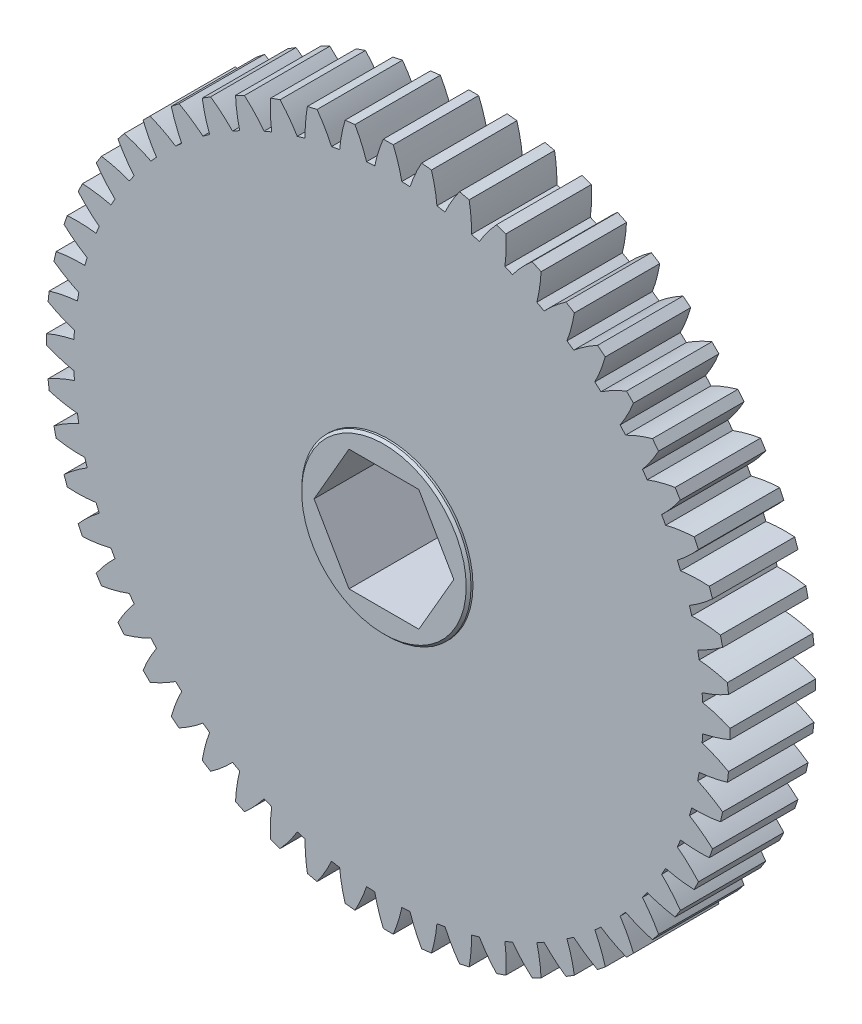
SolidWorks part; units mm, degrees
material "AISI 4130 Steel, normalized at 870C"
ref_plane "Front Plane" through (0, 0, 0) normal (0, 0, 1) x (1, 0, 0)
ref_plane "Top Plane" through (0, 0, 0) normal (0, 1, 0) x (1, 0, 0)
ref_plane "Right Plane" through (0, 0, 0) normal (1, 0, 0) x (0, 0, -1)
sketch "Sketch1" plane through (0, 0, 0) normal (0, 0, 1) x (1, 0, 0)
  circle A0 centre (0, 0) radius 33.02
  dimension "D1" = 66.04
extrude "Extrude1" add sketch "Sketch1" along normal mid plane 8.9662
sketch "Sketch2" plane through (0, 0, -4.4831) normal (0, 0, -1) x (-1, 0, 0)
  line L0 (35.8775, 0.5187) -> (35.8775, -0.5187)
  line L1 (35.8775, 0) -> (33.02, 0) construction
  arc A0 (35.8775, 0.5187) -> (32.9894, 1.4209) centre (29.9148, -13.4957) ccw
  arc A1 (32.9894, -1.4209) -> (35.8775, -0.5187) centre (29.9148, 13.4957) ccw
  circle A2 centre (0, 0) radius 33.02 construction
  arc A3 (32.9894, -1.4209) -> (32.9894, 1.4209) centre (0, 0) ccw
  dimension "D4" = 15.2301
  dimension "D1" = 1.0374
  dimension "D2" = 2.8417
  dimension "D3" = 2.8575
extrude "Extrude2" add sketch "Sketch2" against normal up to surface (8.9662 mm away) up to face at (33.02, 0, 4.4831)
pattern_circular "CirPattern1" count 56 over 360 about axis through (0, 0, 0) along (0, 0, 1) of "Extrude2"
sketch "Sketch6" plane through (0, 0, 0) normal (0, 0, 1) x (1, 0, 0)
  circle A0 centre (0, 0) radius 8.89
  dimension "D1" = 17.78
extrude "Extrude4" add sketch "Sketch6" along normal offset from surface 0.4572 and the other way offset from surface (4.9403 mm away) 0.4572 up to face at (0, 0, 4.4831) offset beyond the face yes
chamfer "Chamfer1" distance 0.254 angle 45 2 edges at (8.89, 0, -4.9403) (8.89, 0, 4.9403)
sketch "Sketch4" plane through (0, 0, 0) normal (0, 0, 1) x (1, 0, 0)
  line L0 (-3.6662, -6.35) -> (3.6662, -6.35)
  line L1 (3.6662, -6.35) -> (7.3323, 0)
  line L2 (7.3323, 0) -> (3.6662, 6.35)
  line L3 (3.6662, 6.35) -> (-3.6662, 6.35)
  line L4 (-3.6662, 6.35) -> (-7.3323, 0)
  line L5 (-7.3323, 0) -> (-3.6662, -6.35)
  circle A0 centre (0, 0) radius 6.35 construction
  dimension "D1" = 12.7
extrude "Extrude3" cut sketch "Sketch4" against normal through all and the other way through all
